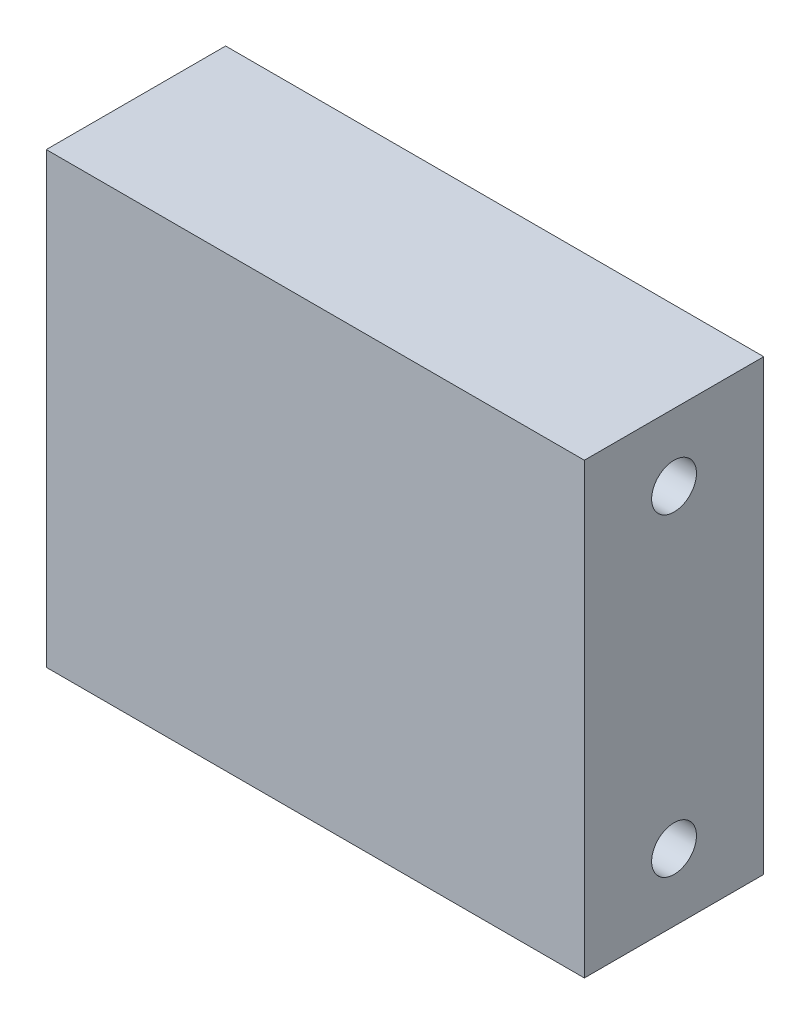
SolidWorks part; units mm, degrees
ref_plane "Front Plane" through (0, 0, 0) normal (0, 0, 1) x (1, 0, 0)
ref_plane "Top Plane" through (0, 0, 0) normal (0, 1, 0) x (1, 0, 0)
ref_plane "Right Plane" through (0, 0, 0) normal (1, 0, 0) x (0, 0, -1)
sketch "Sketch1" plane through (0, 0, 0) normal (0, 1, 0) x (1, 0, 0)
  line L1 (0, 0) -> (152.4, 0)
  line L2 (0, 0) -> (0, 50.8)
  line L3 (0, 50.8) -> (152.4, 50.8)
  line L4 (152.4, 0) -> (152.4, 50.8)
  dimension "D1" = 50.8
  dimension "D2" = 152.4
extrude "Boss-Extrude1" add sketch "Sketch1" along normal blind 127
sketch "Sketch2" plane through (152.4, 0, 0) normal (1, 0, 0) x (0, 0, -1)
sketch "Sketch3" plane through (0, 0, 0) normal (-1, 0, 0) x (0, 0, 1)
  line L0 (-25.4, 127) -> (-25.4, 0) construction
  line L1 (-50.8, 127) -> (0, 127) construction
  line L2 (-50.8, 0) -> (0, 0) construction
  line L3 (0, 63.5) -> (-50.8, 63.5) construction
  line L4 (0, 127) -> (0, 0) construction
  line L5 (-50.8, 127) -> (-50.8, 0) construction
  circle A1 centre (-25.4, 19.05) radius 6.35
  circle A2 centre (-25.4, 107.95) radius 6.35
  point P6 (-25.4, 105.8407)
  dimension "D1" = 88.9
  dimension "D2" = 12.7
extrude "Cut-Extrude1" cut sketch "Sketch3" against normal through all
